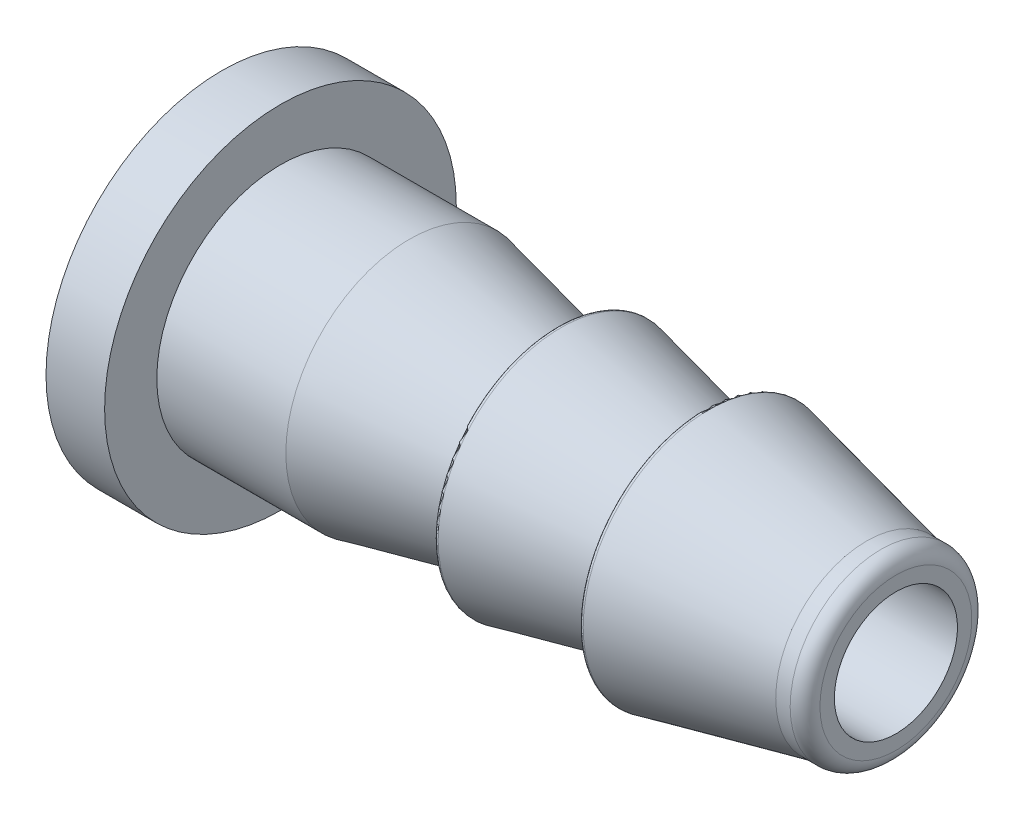
SolidWorks part; units mm, degrees
ref_plane "Front Plane" through (0, 0, 0) normal (0, 0, 1) x (1, 0, 0)
ref_plane "Top Plane" through (0, 0, 0) normal (0, 1, 0) x (1, 0, 0)
ref_plane "Right Plane" through (0, 0, 0) normal (1, 0, 0) x (0, 0, -1)
sketch "Sketch1" plane through (0, 0, 0) normal (0, 0, 1) x (1, 0, 0)
  line L0 (0, 0) -> (8.3844, 0) construction
  line L1 (0, 2.1) -> (8.3844, 2.1)
  line L2 (0, 3.1) -> (14.5, 3.1)
  line L3 (0, 3.1) -> (0, 2.1)
  line L4 (14.5, 3.1) -> (14.5, 4.3193)
  line L6 (21, 2.592) -> (21, 2.1)
  line L7 (21, 2.1) -> (8.3844, 2.1)
  line L8 (14.5, 4.3193) -> (20, 3.1)
  line L9 (20, 3.1) -> (20.492, 3.1)
  line L10 (0, 0) -> (0, 3.1) construction
  arc A0 (21, 2.592) -> (20.492, 3.1) centre (20.492, 2.592) ccw
  point P7 (14.5, 3.7097)
  point P14 (21, 3.1)
  dimension "D6" = 0.508
  dimension "D1" = 3.1
  dimension "D2" = 1
  dimension "D3" = 1
  dimension "D4" = 5.5
  dimension "D5" = 12.5
  dimension "D7" = 21
revolve "Revolve2" add sketch "Sketch1" angle 360 about L0
sketch "Sketch2" plane through (0, 0, 0) normal (-1, 0, 0) x (0, 0, 1)
  circle A0 centre (0, 0) radius 2.1
  circle A1 centre (0, 0) radius 6
  circle A2 centre (0, 0) radius 2.1 construction
  dimension "D1" = 12
extrude "Boss-Extrude1" add sketch "Sketch2" along normal blind 2
sketch "Sketch3" plane through (0, 0, 0) normal (0, 0, 1) x (1, 0, 0)
  line L0 (14.5, 3.1) -> (9.4511, 4.2193)
  line L1 (9.4511, 4.2193) -> (9.4511, 3.1)
  line L2 (14.5, 3.1) -> (0, 3.1) construction
  line L3 (9.4511, 4.2193) -> (14.5, 4.2193) construction
  line L5 (9.4511, 3.1) -> (14.5, 3.1)
  line L9 (0, -6) -> (0, 6) construction
  line L10 (0, 4.2193) -> (0, 3.1)
  line L11 (0, 3.1) -> (9.4511, 3.1)
  line L12 (0, 4.2193) -> (4.4021, 4.2193)
  line L13 (4.4021, 4.2193) -> (9.4511, 3.1)
  line L14 (4.4021, 4.2193) -> (9.4511, 4.2193) construction
  line L15 (-2, 0) -> (21, 0) construction
  line L16 (-2, 6) -> (-2, -6) construction
  line L17 (21, -2.592) -> (21, 2.592) construction
  line L18 (14.5, 4.3193) -> (14.5, -4.3193) construction
  dimension "D2" = 12.5
  dimension "D1" = 12.5
  dimension "D3" = 0.1
revolve "Revolve3" add sketch "Sketch3" angle 360 about L15
fillet "Fillet1" radius 0.1 2 edges at (9.4511, 0, 4.2193) (14.5, 0, 4.3193)
fillet "Fillet2" radius 0.3 2 edges at (9.4511, 0, 3.1) (14.5, 0, 3.1)
